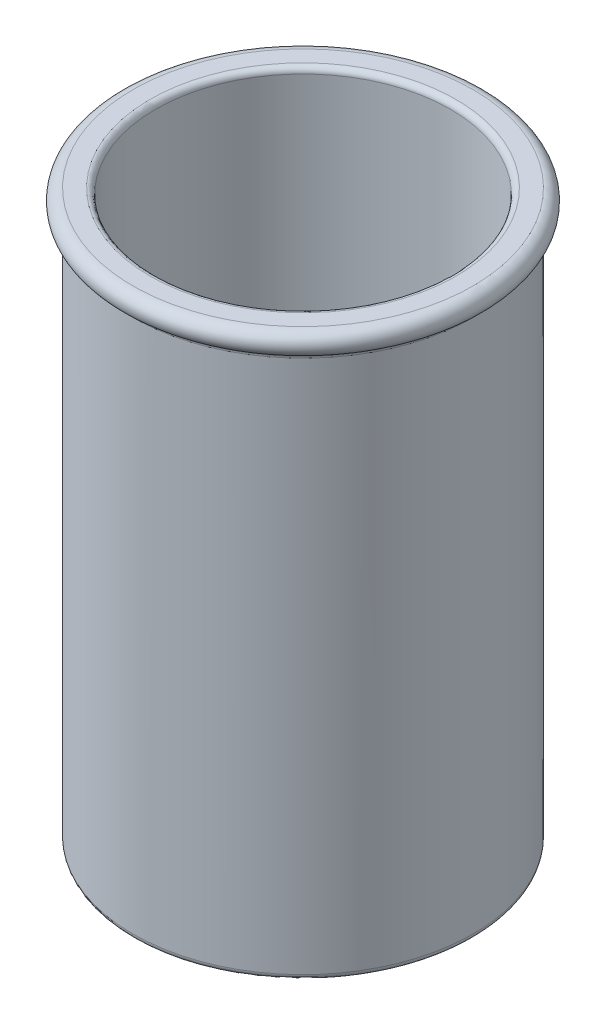
SolidWorks part; units mm, degrees
ref_plane "Front Plane" through (0, 0, 0) normal (0, 0, 1) x (1, 0, 0)
ref_plane "Top Plane" through (0, 0, 0) normal (0, 1, 0) x (1, 0, 0)
ref_plane "Right Plane" through (0, 0, 0) normal (1, 0, 0) x (0, 0, -1)
sketch "Base" plane through (0, 0, 0) normal (0, 1, 0) x (1, 0, 0)
  circle A0 centre (0, 0) radius 15
  dimension "D1" = 30
extrude "Boss-Extrude1" add sketch "Base" along normal blind 2
sketch "Sketch2" plane through (0, 2, 0) normal (0, 1, 0) x (1, 0, 0)
  circle A0 centre (0, 0) radius 15 construction
  circle A1 centre (0, 0) radius 15
  circle A2 centre (0, 0) radius 13
  dimension "D1" = 2
extrude "Boss-Extrude2" add sketch "Sketch2" along normal blind 48
sketch "Sketch4" plane through (0, 0, 0) normal (0, 0, 1) x (1, 0, 0)
  line L0 (15, 50) -> (15, 48)
  arc A0 (15, 48) -> (15, 50) centre (15, 49) ccw
sketch "Sketch5" plane through (0, 0, 0) normal (0, 0, 1) x (1, 0, 0)
  line L0 (0, 0) -> (0, 50) construction
  line L1 (0, 25) -> (15, 25) construction
  line L2 (15, 0) -> (15, 50) construction
revolve "Revolve3" add sketch "Sketch4" angle 360 about L0
sketch "Sketch7" plane through (0, 0, 0) normal (1, 0, 0) x (0, 0, -1)
  line L0 (0, 0) -> (0, 50) construction
  line L1 (0, 0) -> (0, 50) construction
  line L2 (0, 25) -> (15, 25) construction
  line L3 (15, 0) -> (15, 48) construction
sketch3d "3DSketch2"
  line L0 (0, 25, 0) -> (0, 25, -15) construction
  line L1 (0, 25, 0) -> (15, 25, 0) construction
fillet "Fillet1" radius 0.5 1 edges at (0, 0, 15)
fillet "Fillet2" radius 0.5 1 edges at (0, 50, 13)
fillet "Fillet4" radius 0.5 1 edges at (0, 48, -15)
